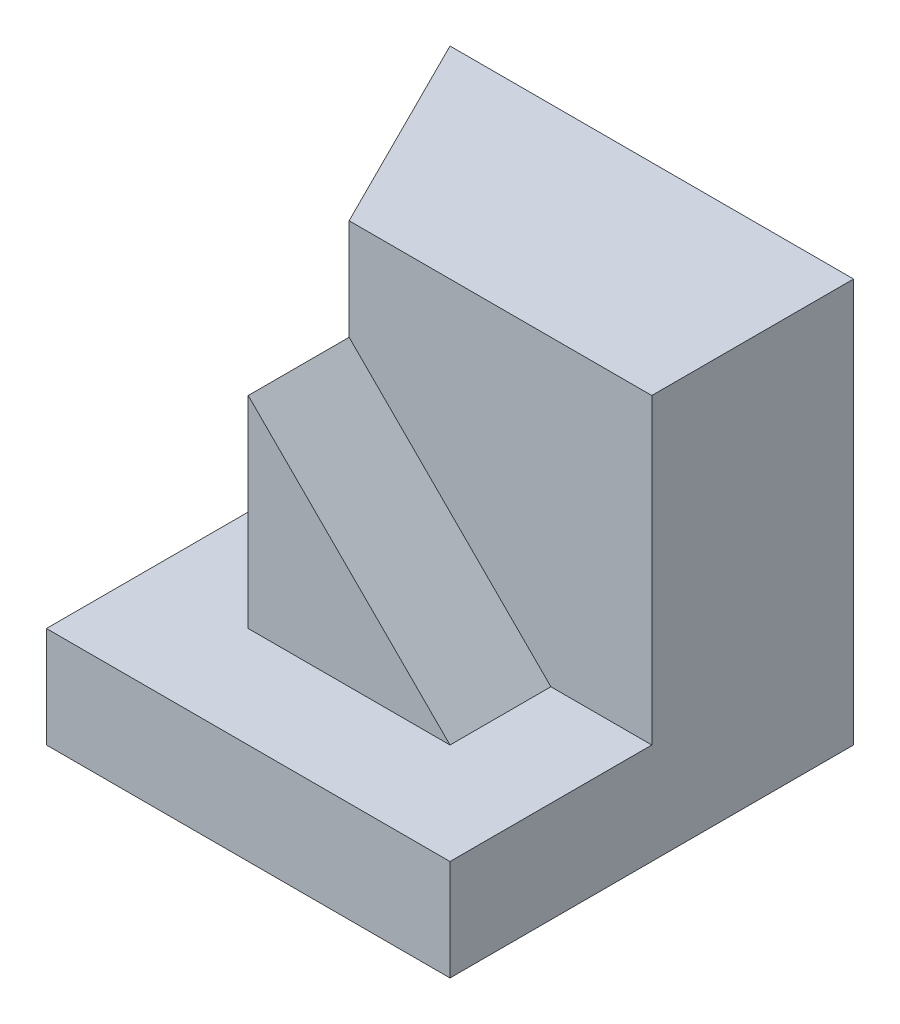
SolidWorks part; units mm, degrees
ref_plane "Front Plane" through (0, 0, 0) normal (0, 0, 1) x (1, 0, 0)
ref_plane "Top Plane" through (0, 0, 0) normal (0, 1, 0) x (1, 0, 0)
ref_plane "Right Plane" through (0, 0, 0) normal (1, 0, 0) x (0, 0, -1)
sketch "Sketch1" plane through (0, 0, 0) normal (0, 0, 1) x (1, 0, 0)
  line L1 (0, 0) -> (40, 0)
  line L2 (0, 0) -> (0, 40)
  line L3 (0, 40) -> (40, 40)
  line L4 (40, 0) -> (40, 40)
  dimension "D1" = 40
  dimension "D2" = 40
extrude "Boss-Extrude1" add sketch "Sketch1" along normal blind 40
sketch "Sketch2" plane through (0, 0, 0) normal (-1, 0, 0) x (0, 0, 1)
  line L1 (40, 40) -> (30, 40)
  line L2 (40, 40) -> (40, 10)
  line L3 (40, 10) -> (30, 10)
  line L4 (30, 40) -> (30, 10)
  line L5 (30, 40) -> (20, 40)
  line L6 (30, 40) -> (30, 30)
  line L7 (30, 30) -> (20, 30)
  line L8 (20, 40) -> (20, 30)
  line M3 (40, 0) -> (40, 40)
  line M4 (40, 40) -> (0, 40)
  dimension "D1" = 10
  dimension "D2" = 30
  dimension "D3" = 10
  dimension "D4" = 10
extrude "Cut-Extrude1" cut sketch "Sketch2" against normal blind 40 contours L8 L7 L4 M4 | L4 L3 M4 M3
sketch "Sketch3" plane through (0, 30, 0) normal (0, 1, 0) x (1, 0, 0)
  line L0 (40, -30) -> (0, -30) construction
  line L1 (40, -20) -> (30, -20)
  line L2 (40, -20) -> (40, -30)
  line L3 (40, -30) -> (30, -30)
  line L4 (30, -20) -> (30, -30)
  dimension "D1" = 10
extrude "Cut-Extrude2" cut sketch "Sketch3" against normal blind 20
sketch "Sketch5" plane through (0, 30, 0) normal (0, 1, 0) x (1, 0, 0)
  line L0 (30, -20) -> (0, -20) construction
  line L1 (0, -30) -> (10, -30)
  line L2 (0, -30) -> (0, -20)
  line L3 (0, -20) -> (10, -20)
  line L4 (10, -30) -> (10, -20)
  dimension "D1" = 10
extrude "Cut-Extrude3" cut sketch "Sketch5" against normal blind 20
sketch "Sketch6" plane through (0, 40, 0) normal (0, 1, 0) x (1, 0, 0)
  line L0 (10, -20) -> (0, 0)
  line L1 (40, -20) -> (0, -20) construction
  line L2 (0, 0) -> (0, -20)
  line L3 (0, -20) -> (10, -20)
  dimension "D1" = 10
extrude "Cut-Extrude5" cut sketch "Sketch6" against normal blind 30
sketch "Sketch7" plane through (0, 0, 30) normal (0, 0, 1) x (1, 0, 0)
  line L0 (10, 30) -> (30, 10)
  line L1 (30, 10) -> (30, 30)
  line L2 (30, 30) -> (10, 30)
extrude "Cut-Extrude6" cut sketch "Sketch7" against normal blind 10
